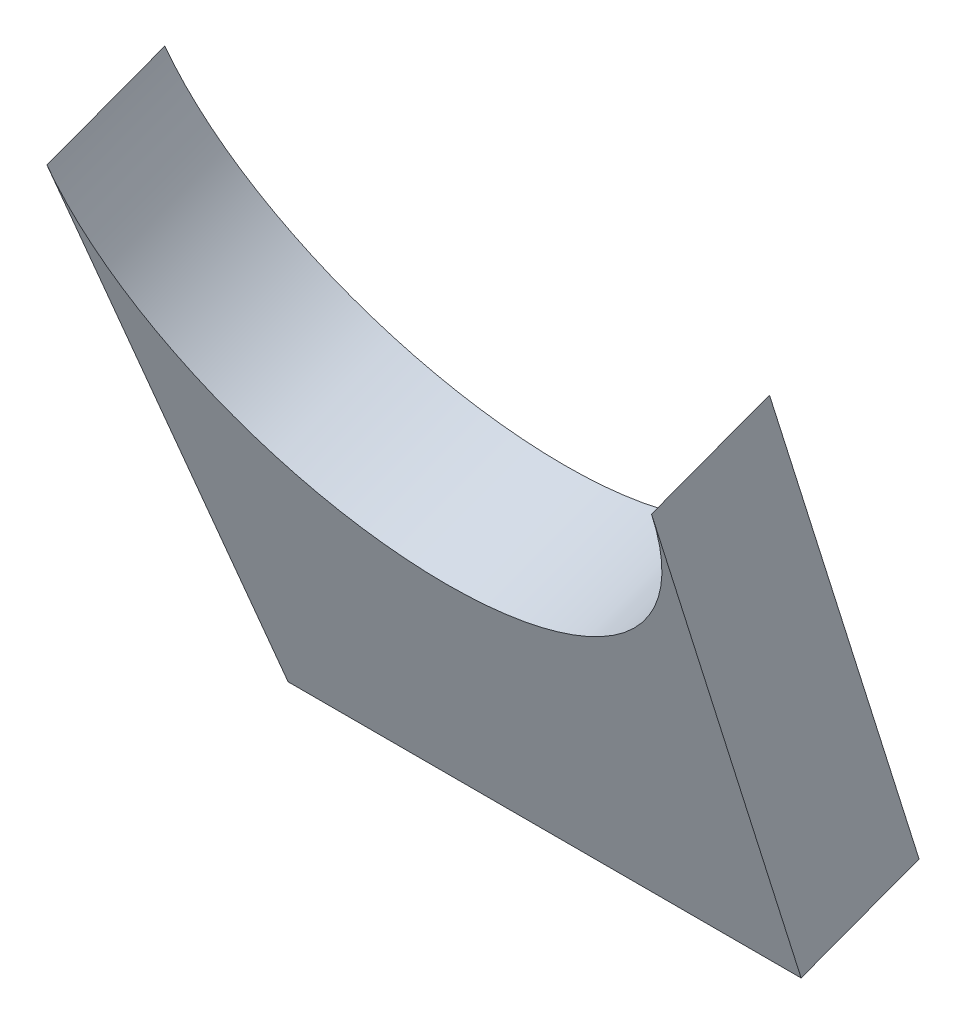
SolidWorks part; units mm, degrees
ref_plane "Front Plane" through (0, 0, 0) normal (0, 0, 1) x (1, 0, 0)
ref_plane "Top Plane" through (0, 0, 0) normal (0, 1, 0) x (1, 0, 0)
ref_plane "Right Plane" through (0, 0, 0) normal (1, 0, 0) x (0, 0, -1)
sketch3d "3DSketch2"
  line L0 (256.7061, 579.7535, 365.9722) -> (216.7011, 123.5793, 195.3325) construction
  line L1 (216.7011, 123.5793, 195.3325) -> (256.7061, 579.7535, 365.9722) construction
  line L2 (77.0011, 123.5793, 195.3325) -> (36.9961, 579.7535, 365.9722) construction
  line L3 (77.0011, 123.5793, 195.3325) -> (216.7011, 123.5793, 195.3325) construction
  line L4 (216.7011, 123.5793, 195.3325) -> (229.1769, 265.8405, 248.5477) construction
  line L5 (77.0011, 123.5793, 195.3325) -> (64.5252, 265.8405, 248.5477) construction
  circle A0 centre (77.0011, 123.5793, 195.3325) radius 17.145 construction
  circle A1 centre (36.9961, 579.7535, 365.9722) radius 17.145 construction
  arc A3 (64.5252, 265.8405, 248.5477) -> (229.1769, 265.8405, 248.5477) centre (146.8511, 272.174, 250.9169) cw construction
  point P8 (78.4046, 107.5749, 189.3458)
  point P11 (38.3996, 563.7491, 359.9855)
  point P15 (146.8511, 243.2334, 328.2843)
  dimension "D1" = 152.4
  dimension "D2" = 152.4
ref_plane "Plane1" through (0, -48.929, 130.8029) normal (0, -0.3504, 0.9366) x (1, 0, 0)
sketch "Sketch4" plane through (0, -48.929, 130.8029) normal (0, -0.3504, 0.9366) x (1, 0, 0)
  line L0 (64.5252, 336.071) -> (77.0011, 184.1825)
  line L4 (216.7011, 184.1825) -> (229.1769, 336.071)
  line L5 (77.0011, 184.1825) -> (216.7011, 184.1825)
  arc A0 (64.5252, 336.071) -> (229.1769, 336.071) centre (146.8511, 342.8331) ccw
extrude "Boss-Extrude3" add sketch "Sketch4" along normal blind 34.29
